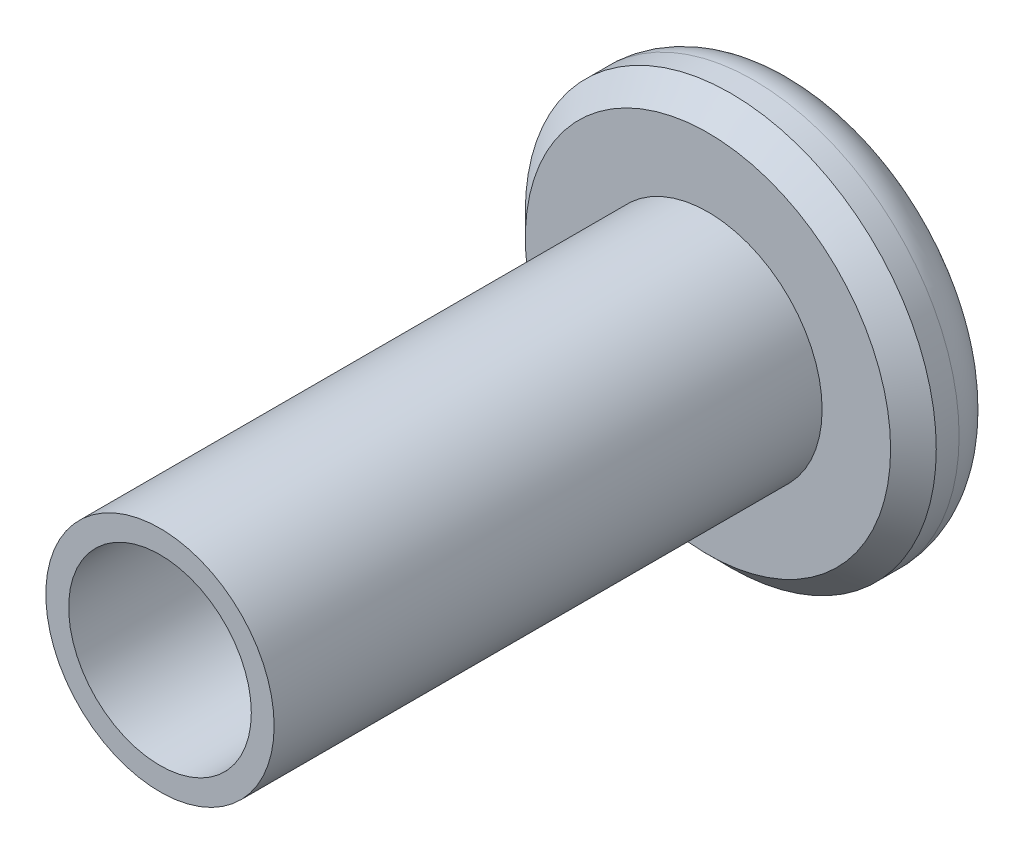
SolidWorks part; units mm, degrees
material "AISI 304"
ref_plane "前视基准面" through (0, 0, 0) normal (0, 0, 1) x (1, 0, 0)
ref_plane "上视基准面" through (0, 0, 0) normal (0, 1, 0) x (1, 0, 0)
ref_plane "右视基准面" through (0, 0, 0) normal (1, 0, 0) x (0, 0, -1)
sketch "草图1" plane through (0, 0, 0) normal (0, 0, 1) x (1, 0, 0)
  circle A0 centre (0, 0) radius 4.5
  dimension "D1" = 9
extrude "凸台-拉伸1" add sketch "草图1" along normal blind 2
sketch "草图2" plane through (0, 0, 2) normal (0, 0, 1) x (1, 0, 0)
  circle A0 centre (0, 0) radius 2.5
  circle A1 centre (0, 0) radius 2
  dimension "D1" = 5
  dimension "D2" = 4
extrude "凸台-拉伸2" add sketch "草图2" along normal blind 12
fillet "圆角1" radius 1 1 edges at (4.5, 0, 0)
chamfer "倒角1" distance 0.5 angle 45 1 edges at (4.5, 0, 2)
sketch "草图3" plane through (0, 0, 0) normal (0, 0, -1) x (-1, 0, 0)
  line L1 (0.866, -1.5) -> (1.7321, 0)
  line L2 (1.7321, 0) -> (0.866, 1.5)
  line L3 (0.866, 1.5) -> (-0.866, 1.5)
  line L4 (-0.866, 1.5) -> (-1.7321, 0)
  line L5 (-1.7321, 0) -> (-0.866, -1.5)
  line L6 (-0.866, -1.5) -> (0.866, -1.5)
  circle A0 centre (0, 0) radius 1.5 construction
  dimension "D1" = 3
extrude "切除-拉伸1" cut sketch "草图3" against normal blind 1
